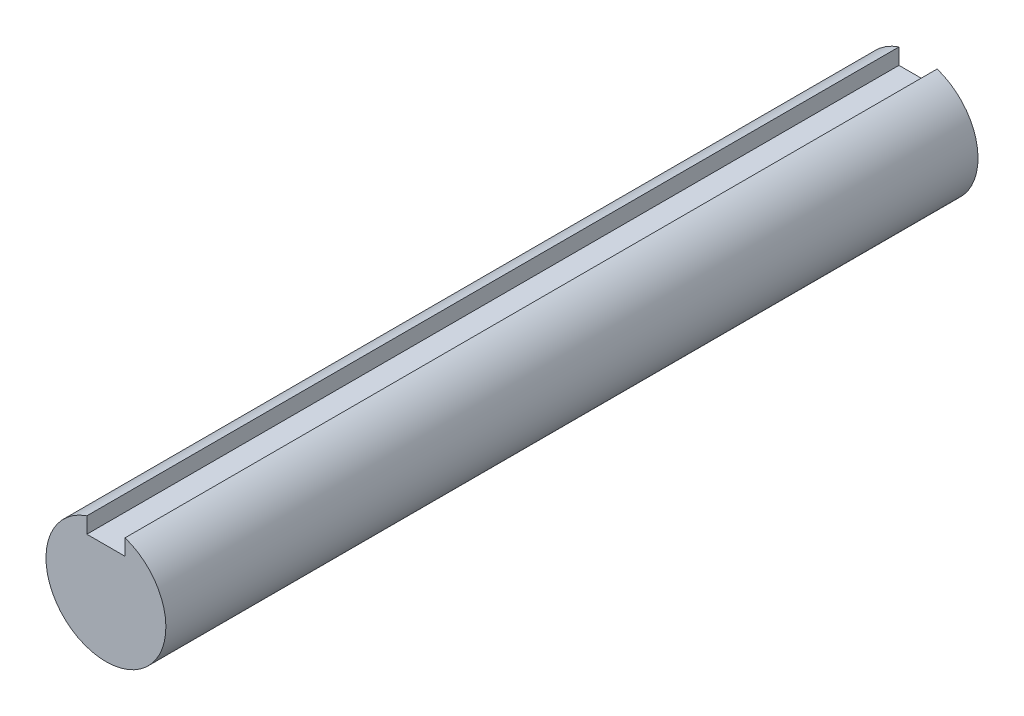
SolidWorks part; units mm, degrees
ref_plane "Front" through (0, 0, 0) normal (0, 0, 1) x (1, 0, 0)
ref_plane "Top" through (0, 0, 0) normal (0, 1, 0) x (1, 0, 0)
ref_plane "Right" through (0, 0, 0) normal (1, 0, 0) x (0, 0, -1)
sketch "Sketch1" plane through (0, 0, 0) normal (0, 0, 1) x (1, 0, 0)
  circle A0 centre (0, 0) radius 7.5
  dimension "dia" = 15
extrude "Extrude1" add sketch "Sketch1" along normal mid plane 101.6
sketch "Sketch2" plane through (0, 0, 0) normal (1, 0, 0) x (0, 0, -1)
  point P0 (-50.8, 7.5)
  point P1 (50.8, 7.5)
  point P2 (50.8, -7.5)
sketch "Sketch3" plane through (0, 0, 0) normal (0, 0, 1) x (1, 0, 0)
  line L1 (-2.3876, 7.9375) -> (2.3876, 7.9375)
  line L2 (-2.3876, 7.9375) -> (-2.3876, 5.113)
  line L3 (-2.3876, 5.113) -> (2.3876, 5.113)
  line L4 (2.3876, 7.9375) -> (2.3876, 5.113)
  dimension "D1" = 7.9375
  dimension "D2" = 4.7752
  dimension "D3" = 2.8245
  dimension "D4" = 2.3876
extrude "Extrude2" cut sketch "Sketch3" against normal through all and the other way through all
